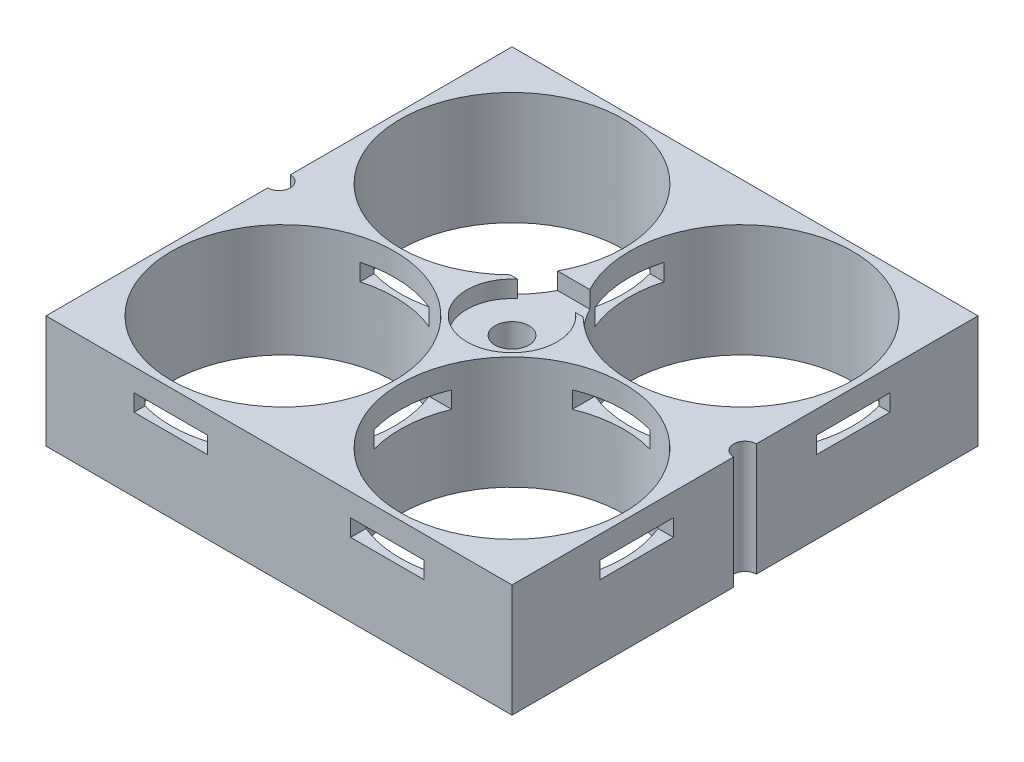
SolidWorks part; units mm, degrees
ref_plane "Front Plane" through (0, 0, 0) normal (0, 0, 1) x (1, 0, 0)
ref_plane "Top Plane" through (0, 0, 0) normal (0, 1, 0) x (1, 0, 0)
ref_plane "Right Plane" through (0, 0, 0) normal (1, 0, 0) x (0, 0, -1)
sketch "Croquis1" plane through (0, 0, 0) normal (0, 1, 0) x (1, 0, 0)
  line L0 (0, 0) -> (0, 20.65) construction
  line L1 (-20.65, 20.65) -> (20.65, 20.65)
  line L2 (-20.65, 20.65) -> (-20.65, -20.65)
  line L3 (-20.65, -20.65) -> (20.65, -20.65)
  line L4 (20.65, 20.65) -> (20.65, -20.65)
  line L5 (0, 0) -> (20.65, 0) construction
  line L7 (-10.15, 10.15) -> (10.15, 10.15) construction
  line L8 (-10.15, 10.15) -> (-10.15, -10.15) construction
  line L9 (-10.15, -10.15) -> (10.15, -10.15) construction
  line L10 (10.15, 10.15) -> (10.15, -10.15) construction
  circle A0 centre (-20.65, 0) radius 1
  circle A1 centre (20.65, 0) radius 1
  circle A2 centre (-10.15, 10.15) radius 9.9
  circle A3 centre (10.15, 10.15) radius 9.9
  circle A4 centre (10.15, -10.15) radius 9.9
  circle A5 centre (-10.15, -10.15) radius 9.9
  point P19 (0, 10.15)
  point P20 (10.15, 0)
  dimension "D2" = 2
  dimension "D3" = 19.8
  dimension "D1" = 41.3
  dimension "D4" = 20.3
  dimension "D5" = 20.3
extrude "Saliente-Extruir1" add sketch "Croquis1" along normal blind 10 contours A1 L4 L1 L2 A0 L3 A5 A4 A3 A2
sketch "Croquis3" plane through (0, 0, 20.65) normal (0, 0, 1) x (1, 0, 0)
  line L0 (-9.6, 6.5) -> (-9.6, 1.9968) construction
  line L1 (-12.85, 8) -> (-6.35, 8)
  line L2 (-12.85, 8) -> (-12.85, 6.5)
  line L3 (-12.85, 6.5) -> (-6.35, 6.5)
  line L4 (-6.35, 8) -> (-6.35, 6.5)
  line L5 (6.35, 8) -> (12.85, 8)
  line L6 (6.35, 8) -> (6.35, 6.5)
  line L7 (6.35, 6.5) -> (12.85, 6.5)
  line L8 (12.85, 8) -> (12.85, 6.5)
  line L9 (9.6, 6.5) -> (9.6, 1.9968) construction
  line L10 (-9.6, 1.9968) -> (9.6, 1.9968) construction
  line L11 (-20.65, 10) -> (20.65, 10) construction
  line L12 (-20.65, 0) -> (20.65, 0) construction
  line L13 (0, 1.9968) -> (0, 0) construction
  point P18 (9.6, 7.3)
  dimension "D1" = 6.5
  dimension "D2" = 1.5
  dimension "D3" = 19.2
  dimension "D4" = 2
extrude "Cortar-Extruir1" cut sketch "Croquis3" against normal blind 26
sketch "Croquis4" plane through (0, 0, 0) normal (1, 0, 0) x (0, 0, -1)
  line L0 (0, 25.4697) -> (0, 0) construction
pattern_circular "MatrizC1" count 2 every 90 about axis through (0, 25.4697, 0) along (0, -1, 0) of "Cortar-Extruir1"
sketch "Croquis5" plane through (0, 10, 0) normal (0, 1, 0) x (1, 0, 0)
  line L1 (5.1316, 5.4661) -> (-5.686, 5.4661)
  line L2 (5.1316, 5.4661) -> (5.1316, 3.0685)
  line L3 (5.1316, 3.0685) -> (-5.686, 3.0685)
  line L4 (-5.686, 5.4661) -> (-5.686, 3.0685)
  circle A0 centre (0, 0) radius 4
  circle M8 centre (10.15, 10.15) radius 9.9
  circle M9 centre (-10.15, 10.15) radius 9.9
  dimension "D1" = 8
extrude "Cortar-Extruir3" cut sketch "Croquis5" against normal blind 1.5 contours L3 A0 | A0 L3 L1 M8 M9 | L3 A0
sketch "Croquis6" plane through (0, 8.5, 0) normal (0, 1, 0) x (1, 0, 0)
  circle A0 centre (0, 0) radius 1.5
  dimension "D1" = 3
extrude "Cortar-Extruir4" cut sketch "Croquis6" against normal blind 48.5
